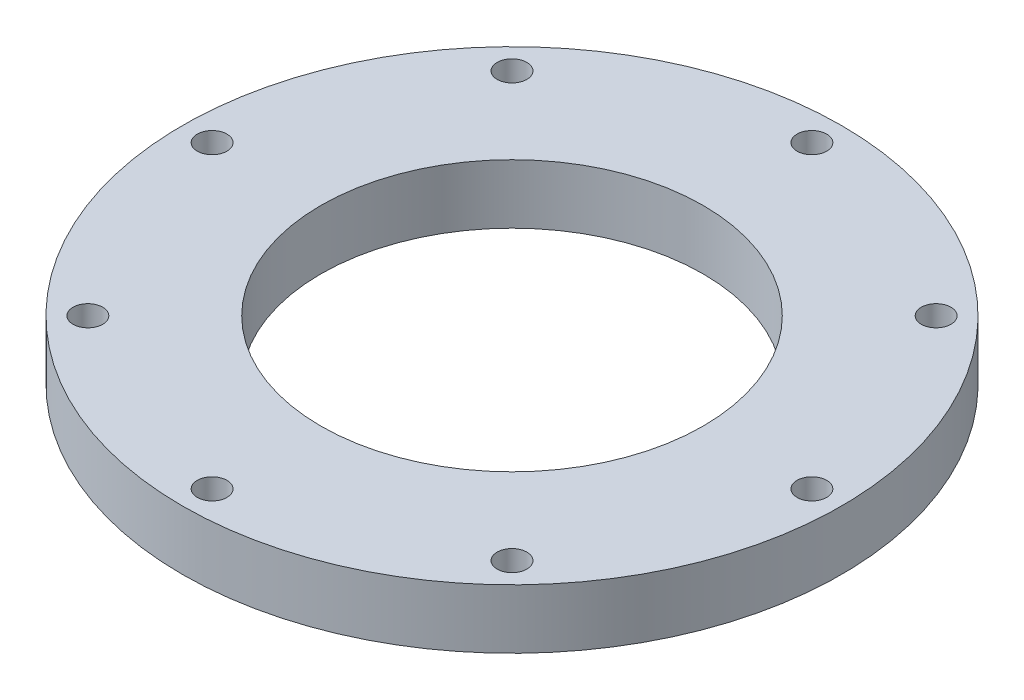
SolidWorks part; units mm, degrees
ref_plane "Front Plane" through (0, 0, 0) normal (0, 0, 1) x (1, 0, 0)
ref_plane "Top Plane" through (0, 0, 0) normal (0, 1, 0) x (1, 0, 0)
ref_plane "Right Plane" through (0, 0, 0) normal (1, 0, 0) x (0, 0, -1)
sketch "Sketch1" plane through (0, 0, 0) normal (0, 1, 0) x (1, 0, 0)
  circle A0 centre (0, 0) radius 29
  circle A1 centre (0, 0) radius 50
  dimension "D1" = 58
  dimension "D2" = 100
extrude "Boss-Extrude1" add sketch "Sketch1" along normal mid plane 9
sketch "Sketch2" plane through (0, 4.5, 0) normal (0, 1, 0) x (1, 0, 0)
  line L0 (0, 0) -> (0, 45.5) construction
  circle A0 centre (0, 0) radius 45.5 construction
  circle A1 centre (0, 45.5) radius 2.25
  dimension "D1" = 91
  dimension "D2" = 4.5
extrude "Cut-Extrude1" cut sketch "Sketch2" against normal through all
pattern_circular "CirPattern1" count 8 over 360 about axis through (0, 0, 0) along (0, 1, 0) of "Cut-Extrude1"
